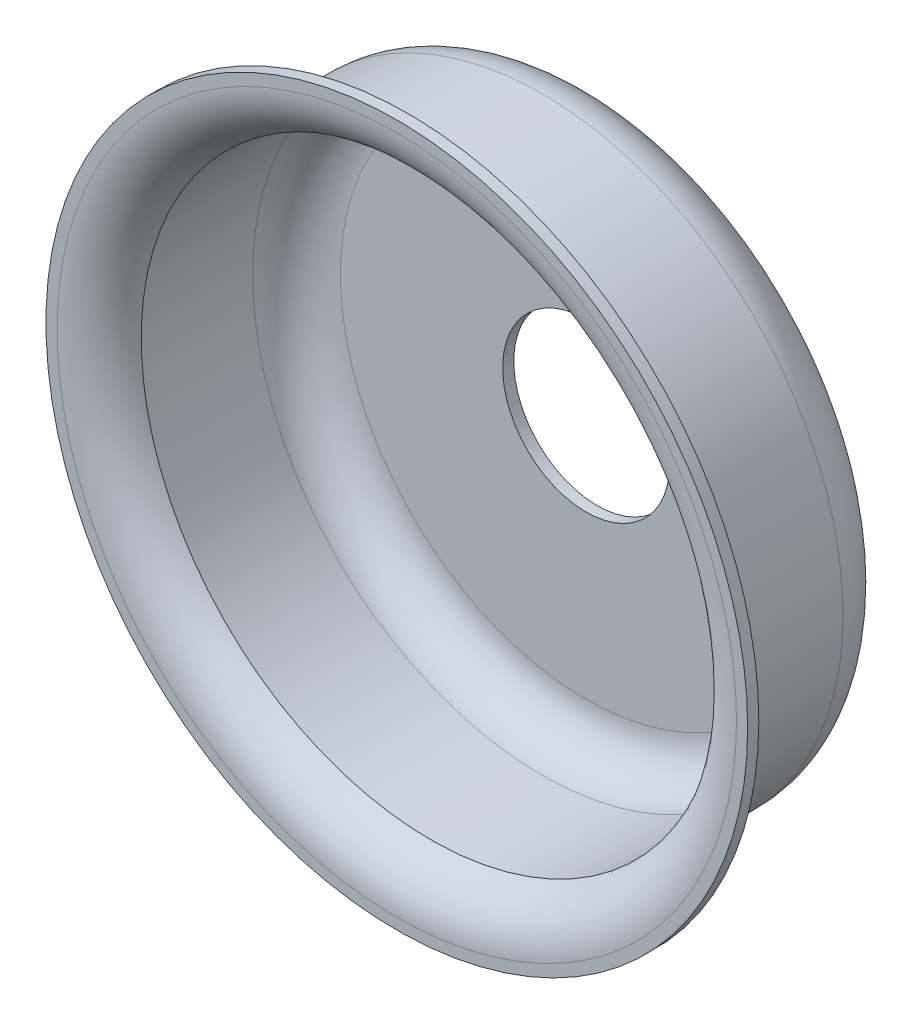
SolidWorks part; units mm, degrees
material "Nickel"
ref_plane "Front Plane" through (0, 0, 0) normal (0, 0, 1) x (1, 0, 0)
ref_plane "Top Plane" through (0, 0, 0) normal (0, 1, 0) x (1, 0, 0)
ref_plane "Right Plane" through (0, 0, 0) normal (1, 0, 0) x (0, 0, -1)
sketch "Sketch1" plane through (0, 0, 0) normal (1, 0, 0) x (0, 0, -1)
  line L0 (-11.4444, 0) -> (40.5439, 0) construction
  line L1 (0, 8.001) -> (0, 7.747)
  line L2 (0.7749, 6.604) -> (3.318, 6.604)
  line L3 (4.318, 5.604) -> (4.318, 1.905)
  line L4 (0, 8.001) -> (0.254, 8.001)
  line L5 (0.254, 8.001) -> (0.254, 7.747)
  line L6 (0.7749, 6.858) -> (3.318, 6.858)
  line L7 (4.572, 5.604) -> (4.572, 1.905)
  line L8 (4.572, 1.905) -> (4.318, 1.905)
  arc A0 (0, 7.747) -> (0.7749, 6.604) centre (1.2304, 7.747) ccw
  arc A1 (4.318, 5.604) -> (3.318, 6.604) centre (3.318, 5.604) ccw
  arc A2 (0.254, 7.747) -> (0.7749, 6.858) centre (1.2731, 7.747) ccw
  arc A3 (3.318, 6.858) -> (4.572, 5.604) centre (3.318, 5.604) cw
  point P11 (4.318, 6.604)
  dimension "D1" = 0.254
  dimension "D6" = 1
  dimension "D2" = 8.001
  dimension "D3" = 4.318
  dimension "D4" = 6.604
  dimension "D5" = 1.905
  dimension "D7" = 0.254
  dimension "D8" = 0.254
  dimension "D9" = 0.254
revolve "Revolve1" add sketch "Sketch1" angle 360 about L0
